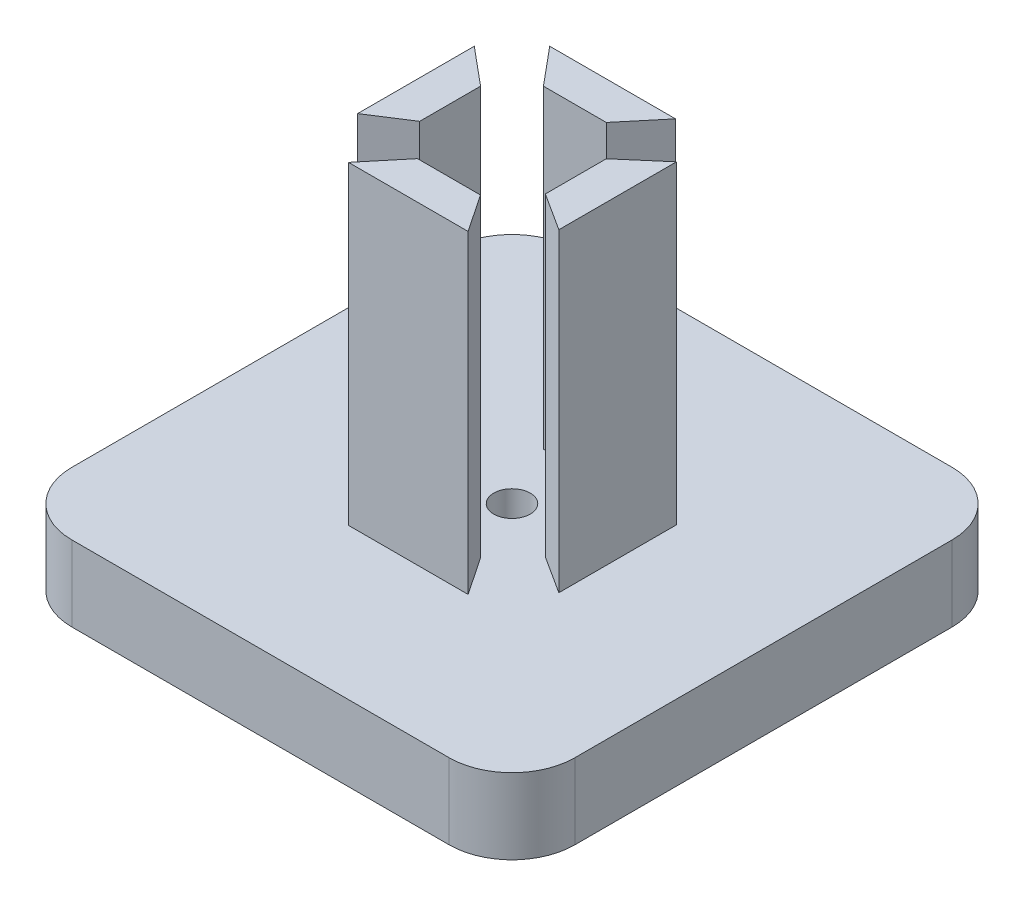
SolidWorks part; units mm, degrees
ref_plane "Front Plane" through (0, 0, 0) normal (0, 0, 1) x (1, 0, 0)
ref_plane "Top Plane" through (0, 0, 0) normal (0, 1, 0) x (1, 0, 0)
ref_plane "Right Plane" through (0, 0, 0) normal (1, 0, 0) x (0, 0, -1)
sketch "Sketch1" plane through (0, 0, 0) normal (0, 1, 0) x (1, 0, 0)
  line L1 (20, -20) -> (-20, -20)
  line L2 (20, -20) -> (20, 20)
  line L3 (20, 20) -> (-20, 20)
  line L4 (-20, -20) -> (-20, 20)
  line L5 (20, -20) -> (-20, 20) construction
  line L6 (20, 20) -> (-20, -20) construction
  point P0 (0, 0)
  dimension "D1" = 40
  dimension "D2" = 40
extrude "Boss-Extrude1" add sketch "Sketch1" along normal blind 6
sketch "Sketch2" plane through (0, 6, 0) normal (0, 1, 0) x (1, 0, 0)
  line L0 (5, 8) -> (-5, 8)
  line L1 (-5, 8) -> (-2.5, 5)
  line L2 (-2.5, 5) -> (2.5, 5)
  line L3 (2.5, 5) -> (5, 8)
  line L4 (20, 20) -> (-20, 20) construction
  point P3 (0, 8)
  dimension "D1" = 12
  dimension "D2" = 3
  dimension "D3" = 5
  dimension "D4" = 10
  dimension "D5" = 5
  dimension "D6" = 2.5
extrude "Boss-Extrude2" add sketch "Sketch2" along normal blind 25
sketch "Sketch4" plane through (0, 6, 0) normal (0, 1, 0) x (1, 0, 0)
  line L0 (-5, -8) -> (4.5142, -8)
  line L1 (4.5142, -8) -> (2.4847, -5)
  line L2 (2.4847, -5) -> (-2.5153, -5)
  line L3 (-2.5153, -5) -> (-5, -8)
  line L4 (-20, -20) -> (20, -20) construction
  point P3 (-0.2429, -8)
  point P8 (-0.0153, -5)
  dimension "D1" = 12
  dimension "D2" = 3
  dimension "D3" = 5
  dimension "D4" = 2.5
extrude "Boss-Extrude3" add sketch "Sketch4" along normal blind 25
sketch "Sketch5" plane through (0, 6, 0) normal (0, 1, 0) x (1, 0, 0)
  line L0 (8, -4.2752) -> (8, 5.0764)
  line L1 (8, 5.0764) -> (5, 2.5)
  line L2 (5, 2.5) -> (5, -2.3472)
  line L3 (5, -2.3472) -> (8, -4.2752)
  line L4 (-8, -4.2752) -> (-8, 5)
  line L5 (-8, 5) -> (-5, 2.5)
  line L6 (-5, 2.5) -> (-5, -2.3472)
  line L7 (-5, -2.3472) -> (-8, -4.2752)
  line L8 (-20, 20) -> (-20, -20) construction
  line L9 (20, -20) -> (20, 20) construction
  point P3 (8, 0.4006)
  point P8 (-8, 0.3624)
  point P15 (5, 0.0764)
  dimension "D1" = 12
  dimension "D2" = 12
  dimension "D3" = 3
  dimension "D4" = 3
  dimension "D5" = 2.5
  dimension "D6" = 5
  dimension "D7" = 2.5
  dimension "D8" = 5
extrude "Boss-Extrude4" add sketch "Sketch5" along normal blind 25
sketch "Sketch6" plane through (0, 6, 0) normal (0, 1, 0) x (1, 0, 0)
  circle A0 centre (0, 0) radius 1.45
  dimension "D1" = 2.9
extrude "Cut-Extrude1" cut sketch "Sketch6" against normal up to next
fillet "Fillet1" radius 5 4 edges at (-20, 3, 20) (-20, 3, -20) (20, 3, 20) (20, 3, -20)
